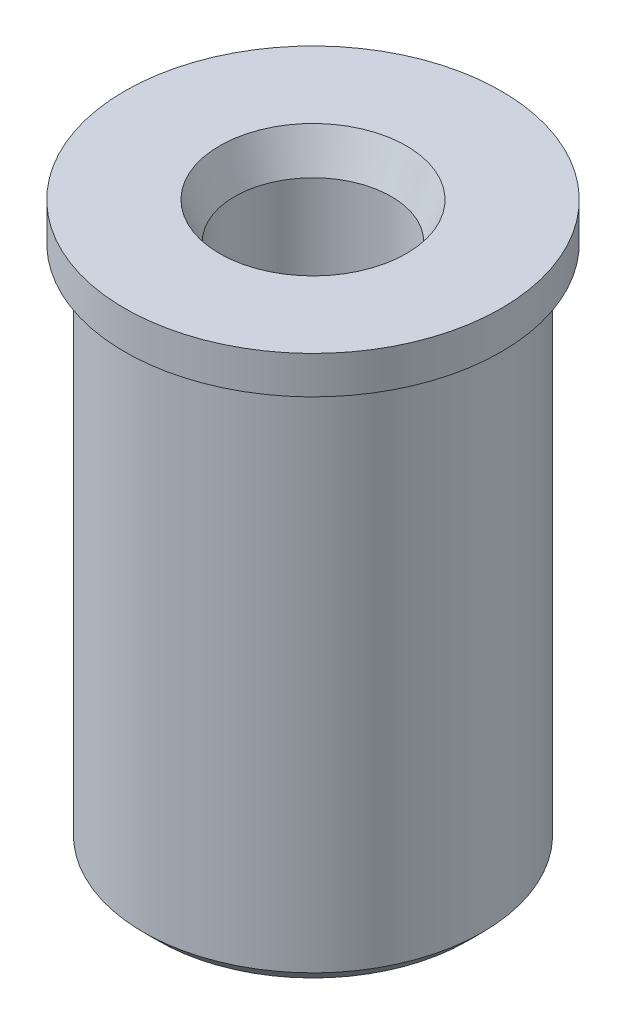
SolidWorks part; units mm, degrees
ref_plane "Front" through (0, 0, 0) normal (0, 0, 1) x (1, 0, 0)
ref_plane "Top" through (0, 0, 0) normal (0, 1, 0) x (1, 0, 0)
ref_plane "Right" through (0, 0, 0) normal (1, 0, 0) x (0, 0, -1)
sketch "Sketch1" plane through (0, 0, 0) normal (0, 0, 1) x (1, 0, 0)
  line L0 (2.8575, 5.715) -> (3.175, 5.715)
  line L1 (-3.175, 5.715) -> (-2.8575, 5.715)
  line L2 (-3.175, 5.715) -> (-3.175, 6.35)
  line L3 (-2.8575, 5.715) -> (-2.8575, 0.254)
  line L4 (-3.175, 6.35) -> (3.175, 6.35)
  line L5 (3.175, 5.715) -> (3.175, 6.35)
  line L6 (2.8575, 5.715) -> (2.8575, 0.254)
  line L7 (2.6035, 0) -> (2.8575, 0.254)
  line L9 (-2.8575, 0.254) -> (-2.6035, 0)
  line L10 (0, 0) -> (0, 6.35) construction
  line L11 (3.175, 5.715) -> (3.175, 6.35)
  line L12 (-3.175, 6.35) -> (3.175, 6.35)
  line L13 (-3.175, 5.715) -> (-3.175, 6.35)
  line L14 (-2.8575, 5.715) -> (-2.8575, -2.921)
  line L15 (-3.175, 5.715) -> (-2.8575, 5.715)
  line L16 (-2.8575, -2.921) -> (-2.6035, -3.175)
  line L17 (-2.6035, -3.175) -> (2.6035, -3.175)
  line L18 (2.8575, 5.715) -> (2.8575, -2.921)
  line L19 (2.6035, -3.175) -> (2.8575, -2.921)
  line L20 (2.8575, 5.715) -> (3.175, 5.715)
  line L21 (0, 0) -> (0, -3.175)
revolve "Revolve1" add sketch "Sketch1" angle 360 about L10
hole_wizard "#6-80 Tapped Hole1" positions "Sketch3" profile "Sketch2" tap size "#0-80" standard "Ansi Inch" end condition through all
sketch "Sketch3" plane through (0, 6.35, 0) normal (0, 1, 0) x (-1, 0, 0)
  point P0 (0, 0)
sketch "Sketch2" plane through (0, 6.35, 0) normal (1, 0, 0) x (0, 0, 1)
  line L0 (0, 0) -> (0, 9.525)
  line L1 (0, 9.525) -> (1.5748, 9.525)
  line L2 (1.3208, 8.9118) -> (1.3208, 0.6132)
  line L3 (1.3208, 0.6132) -> (1.5748, 0)
  line L5 (1.5748, 0) -> (0, 0)
  line L6 (-1.3208, 0.6132) -> (-1.5748, 0) construction
  line L7 (1.5748, 9.525) -> (1.3208, 8.9118)
  line L8 (-1.5748, 9.525) -> (-1.3208, 8.9118) construction
  line L11 (0, -6.35) -> (0, 107.95) construction
  dimension "Thru Tap Drill Dia." = 2.6416
  dimension "Thru Tap Drill Depth" = 9.525
  dimension "Near C'Sink Dia." = 3.1496
  dimension "Near C'Sink Angle" = 45
  dimension "Far C'Sink Dia." = 3.1496
  dimension "Far C'Sink Angle" = 45
cosmetic thread "Hole Thread1" parameters "D2"=2.9972
